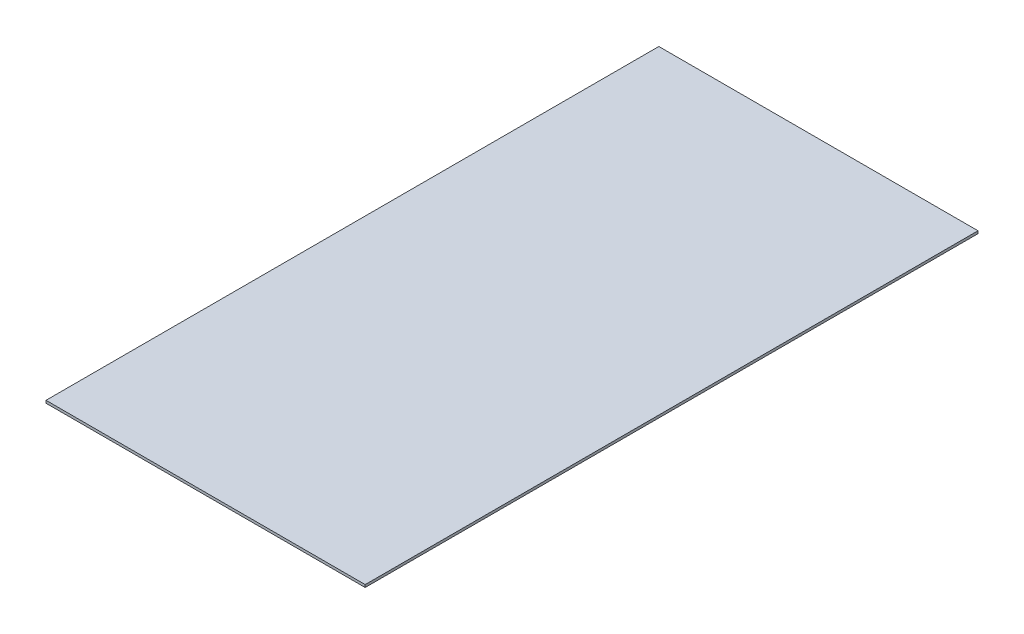
SolidWorks part; units mm, degrees
ref_plane "Front Plane" through (0, 0, 0) normal (0, 0, 1) x (1, 0, 0)
ref_plane "Top Plane" through (0, 0, 0) normal (0, 1, 0) x (1, 0, 0)
ref_plane "Right Plane" through (0, 0, 0) normal (1, 0, 0) x (0, 0, -1)
sketch "Sketch1" plane through (0, 0, 0) normal (0, 1, 0) x (1, 0, 0)
  line L1 (0, 0) -> (317.5, 0)
  line L2 (0, 0) -> (0, 609.6)
  line L3 (0, 609.6) -> (317.5, 609.6)
  line L4 (317.5, 0) -> (317.5, 609.6)
  dimension "D1" = 317.5
  dimension "D2" = 609.6
extrude "Boss-Extrude1" add sketch "Sketch1" along normal blind 2.54
